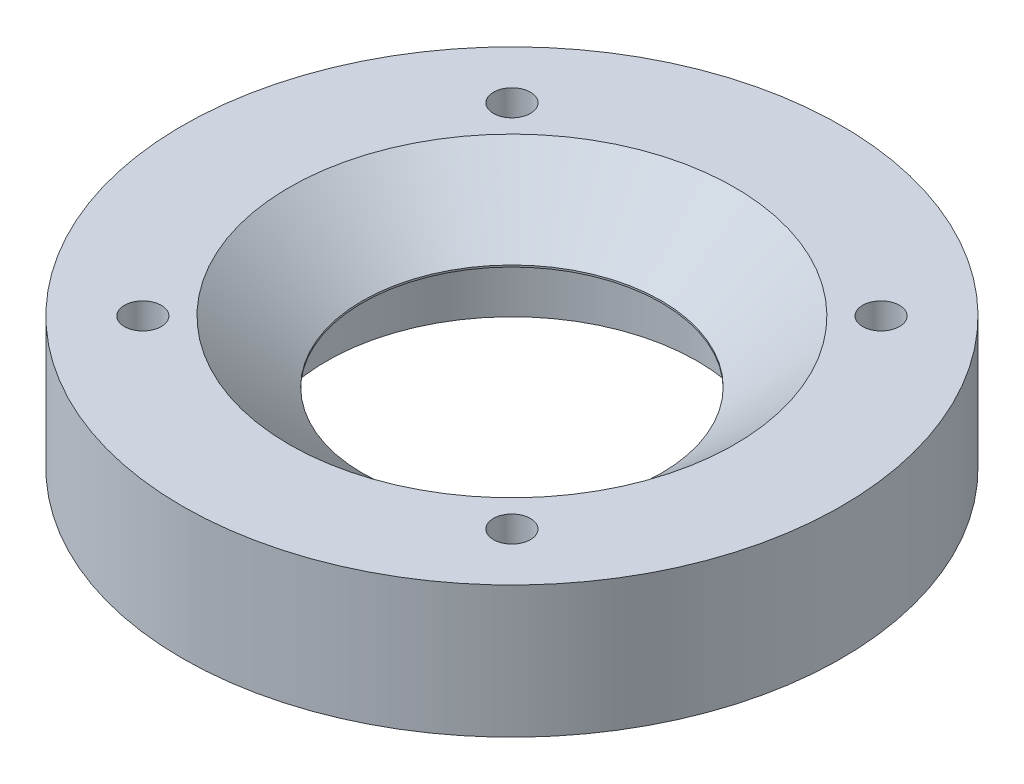
SolidWorks part; units mm, degrees
ref_plane "Спереди" through (0, 0, 0) normal (0, 0, 1) x (1, 0, 0)
ref_plane "Сверху" through (0, 0, 0) normal (0, 1, 0) x (1, 0, 0)
ref_plane "Справа" through (0, 0, 0) normal (1, 0, 0) x (0, 0, -1)
sketch "Sketch1" plane through (0, 0, 0) normal (0, 1, 0) x (1, 0, 0)
  circle A0 centre (0, 0) radius 37.5
  dimension "D1" = 75
extrude "Boss-Extrude1" add sketch "Sketch1" along normal blind 15
sketch "Sketch2" plane through (0, 0, 0) normal (0, -1, 0) x (1, 0, 0)
  circle A0 centre (0, 0) radius 21.1
  dimension "D1" = 42.2
extrude "Cut-Extrude1" cut sketch "Sketch2" against normal blind 7.8
sketch "Sketch3" plane through (0, 7.8, 0) normal (0, -1, 0) x (1, 0, 0)
  circle A0 centre (0, 0) radius 17
  dimension "D1" = 34
extrude "Cut-Extrude2" cut sketch "Sketch3" against normal through all
sketch "Sketch4" plane through (0, 15, 0) normal (0, 1, 0) x (1, 0, 0)
  line L1 (21, 21) -> (-21, 21) construction
  line L2 (21, 21) -> (21, -21) construction
  line L3 (21, -21) -> (-21, -21) construction
  line L4 (-21, 21) -> (-21, -21) construction
  line L5 (21, 21) -> (-21, -21) construction
  line L6 (21, -21) -> (-21, 21) construction
  circle A0 centre (-21, -21) radius 2.1
  circle A1 centre (-21, 21) radius 2.1
  circle A2 centre (21, 21) radius 2.1
  circle A3 centre (21, -21) radius 2.1
  point P0 (0, 0)
  dimension "D2" = 4.2
  dimension "D1" = 42
extrude "Cut-Extrude3" cut sketch "Sketch4" against normal through all
chamfer "Chamfer1" distance 7 angle 50 1 edges at (0, 15, -17)
